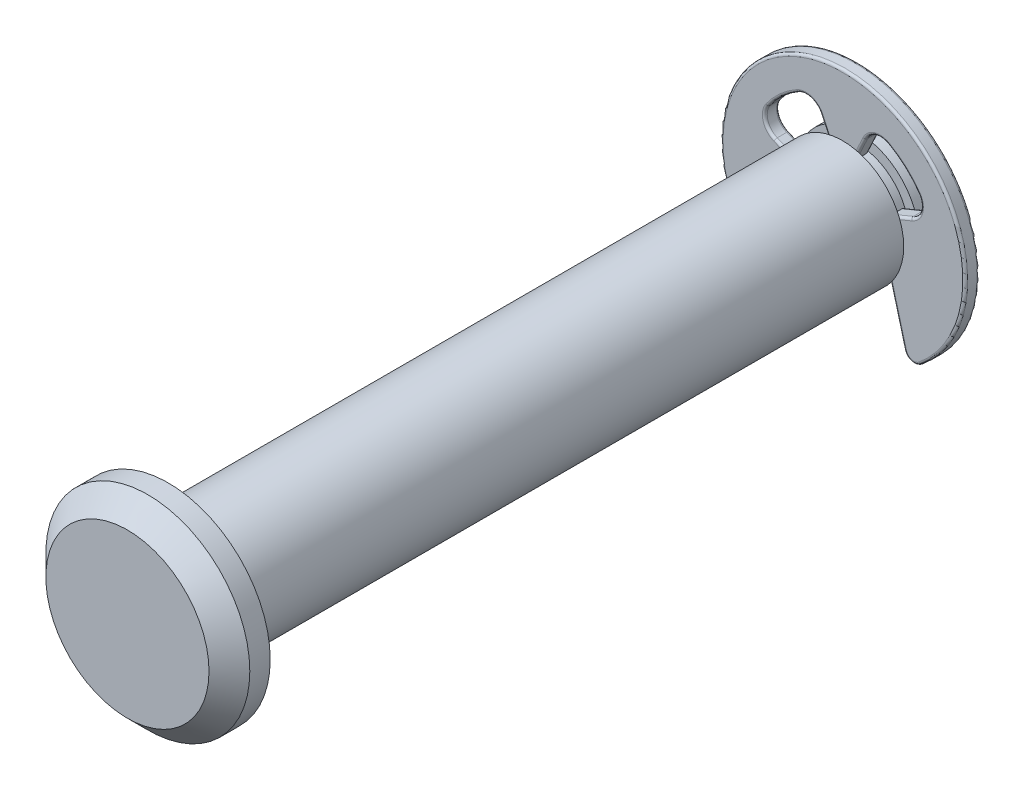
SolidWorks part; units mm, degrees
material "Plain Carbon Steel"
ref_plane "Front Plane" through (0, 0, 0) normal (0, 0, 1) x (1, 0, 0)
ref_plane "Top Plane" through (0, 0, 0) normal (0, 1, 0) x (1, 0, 0)
ref_plane "Right Plane" through (0, 0, 0) normal (1, 0, 0) x (0, 0, -1)
sketch "Sketch1" plane through (0, 0, 0) normal (1, 0, 0) x (0, 0, -1)
  line L0 (-17.5, 0) -> (17.5, 0) construction
  line L1 (-17.5, 0) -> (-19.5, 0) construction
  line L2 (-19.5, 0) -> (-19.5, 4)
  line L3 (-19.5, 4) -> (-18.5, 5)
  line L4 (-18.5, 5) -> (-17.5, 5)
  line L5 (-17.5, 5) -> (-17.5, 3)
  line L6 (-17.5, 3) -> (15.56, 3)
  line L7 (15.56, 3) -> (15.56, 2.5)
  line L8 (15.56, 2.5) -> (16.3, 2.5)
  line L9 (16.3, 2.5) -> (16.3, 3)
  line L10 (16.3, 3) -> (17.5, 3)
  line L11 (17.5, 3) -> (17.5, 0)
  line L12 (15.93, 2.5) -> (15.93, 3) construction
  line L13 (15.58, 0) -> (15.58, 6)
  line L14 (15.58, 6) -> (16.28, 6)
  line L15 (16.28, 6) -> (16.28, 0)
  dimension "Length" = 35
  dimension "Head Height" = 2
  dimension "D1" = 45
  dimension "Head Chamfer Length" = 1
  dimension "Groove Dia" = 5
  dimension "Dia" = 6
  dimension "Head Dia" = 10
  dimension "Ring Dia" = 12
  dimension "Ring Thickness" = 0.7
sketch "Sketch2" plane through (0, 0, 0) normal (1, 0, 0) x (0, 0, -1)
  line L0 (17.5, 3) -> (17.5, 0) construction
  line L1 (16.3, 3) -> (17.5, 3) construction
  line L2 (16.3, 2.5) -> (16.3, 3) construction
  line L3 (15.56, 2.5) -> (16.3, 2.5) construction
  line L4 (15.56, 3) -> (15.56, 2.5) construction
  line L5 (-17.5, 3) -> (15.56, 3) construction
  line L6 (-17.5, 5) -> (-17.5, 3) construction
  line L7 (-18.5, 5) -> (-17.5, 5) construction
  line L8 (-19.5, 4) -> (-18.5, 5) construction
  line L9 (-19.5, 0) -> (-19.5, 4) construction
  line L10 (17.5, 3) -> (17.5, 0)
  line L11 (16.3, 3) -> (17.5, 3)
  line L12 (16.3, 2.5) -> (16.3, 3)
  line L13 (15.56, 2.5) -> (16.3, 2.5)
  line L14 (15.56, 3) -> (15.56, 2.5)
  line L15 (-17.5, 3) -> (15.56, 3)
  line L16 (-17.5, 5) -> (-17.5, 3)
  line L17 (-18.5, 5) -> (-17.5, 5)
  line L18 (-19.5, 4) -> (-18.5, 5)
  line L19 (-19.5, 0) -> (-19.5, 4)
  line L20 (-19.5, 0) -> (17.5, 0)
revolve "Revolve1" add sketch "Sketch2" angle 360 about L0
ref_plane "Plane1" through (0, 0, -15.93) normal (0, 0, -1) x (-1, 0, 0)
sketch "Sketch3" plane through (0, 0, -15.93) normal (0, 0, -1) x (-1, 0, 0)
  line L6 (-1.0931, 3.5605) -> (-0.5681, 2.4346)
  line L7 (0.5681, 2.4346) -> (1.0931, 3.5605)
  line L8 (3.3375, 1.3824) -> (2.3097, 0.9567)
  line L9 (2.1614, -1.2563) -> (3, -4.386)
  line L10 (-3, -4.386) -> (-2.1614, -1.2563)
  line L11 (-2.3097, 0.9567) -> (-3.3375, 1.3824)
  line L12 (0, 0) -> (0, 4.5) construction
  line L13 (0, 0) -> (4.5, 0) construction
  arc A15 (-2.2113, 3.9192) -> (-3.6868, 2.5803) centre (0, 0) ccw
  arc A16 (-1.0931, 3.5605) -> (-2.2113, 3.9192) centre (-1.8182, 3.2225) ccw
  arc A19 (2.2113, 3.9192) -> (1.0931, 3.5605) centre (1.8182, 3.2225) ccw
  arc A20 (3.6868, 2.5803) -> (2.2113, 3.9192) centre (0, 0) ccw
  arc A21 (3.3375, 1.3824) -> (3.6868, 2.5803) centre (3.0313, 2.1215) ccw
  arc A22 (2.1614, -1.2563) -> (2.3097, 0.9567) centre (0, 0) ccw
  arc A23 (3, -4.386) -> (3.7996, -4.6436) centre (3.483, -4.2566) ccw
  arc A26 (-3.7996, -4.6436) -> (-3, -4.386) centre (-3.483, -4.2566) ccw
  arc A27 (-2.3097, 0.9567) -> (-2.1614, -1.2563) centre (0, 0) ccw
  arc A28 (-3.6868, 2.5803) -> (-3.3375, 1.3824) centre (-3.0313, 2.1215) ccw
  circle A30 centre (0, 0) radius 2.5
  circle A31 centre (0, 0) radius 6
  circle A32 centre (0, 0) radius 4.5 construction
  dimension "D1" = 9
  dimension "D6" = 0.5
  dimension "D7" = 0.8
  dimension "D2" = 30
  dimension "D3" = 50
  dimension "D4" = 97.5
  dimension "D8" = 97.5
  dimension "D5" = 6
  dimension "D9" = 3.6364
extrude "Boss-Extrude1" add sketch "Sketch3" along normal up to vertex (0.35 mm away) and the other way up to vertex (0.35 mm away) separate body contours A23 A31 A26 L10 A27 L11 A28 A15 A16 L6 A30 L7 A19 A20 A21 L8 A22 L9 up to point (0, 6, -16.28) other way up to point (0, 6, -15.58)
fillet "Fillet1" radius 0.12 36 edges at (0, 6, -15.58) (3.3297, -4.7326, -15.58) (2.5807, -2.8212, -15.58) (2.4944, -0.1672, -15.58) (2.8236, 1.1696, -15.58) (3.7994, 1.8976, -15.58) (3.0241, 3.3324, -15.58) (1.5738, 3.9842, -15.58) (0.8306, 2.9976, -15.58) (0, 2.5, -15.58) (-0.8306, 2.9976, -15.58) (-1.5738, 3.9842, -15.58) (-3.0241, 3.3324, -15.58) (-3.7994, 1.8976, -15.58) (-2.8236, 1.1696, -15.58) (-2.4944, -0.1672, -15.58) (-2.5807, -2.8212, -15.58) (-3.3297, -4.7326, -15.58) (-2.5807, -2.8212, -16.28) (-2.4944, -0.1672, -16.28) (-2.8236, 1.1696, -16.28) (-3.7994, 1.8976, -16.28) (-3.0241, 3.3324, -16.28) (-1.5738, 3.9842, -16.28) (-0.8306, 2.9976, -16.28) (0, 2.5, -16.28) (0.8306, 2.9976, -16.28) (1.5738, 3.9842, -16.28) (3.0241, 3.3324, -16.28) (3.7994, 1.8976, -16.28) (2.8236, 1.1696, -16.28) (2.4944, -0.1672, -16.28) (2.5807, -2.8212, -16.28) (3.3297, -4.7326, -16.28) (0, 6, -16.28) (-3.3297, -4.7326, -16.28)
chamfer "Chamfer1" distance 0.6 angle 45 1 edges at (3, 0, -17.5)
equation "\"D1@Sketch3\"=\"Ring Dia@Sketch1\"*.75"
equation "\"D6@Sketch3\" = \"Ring Dia@Sketch1\" / 24"
equation "\"D7@Sketch3\" = \"Ring Dia@Sketch1\" / 15"
equation "\"D5@Sketch3\" = \"Ring Dia@Sketch1\" / 2"
equation "\"D9@Sketch3\"= \"Ring Dia@Sketch1\" / 3.3"
equation "\"D1@Fillet1\"=\"Ring Dia@Sketch1\"*.01"
equation "\"D1@Chamfer1\"=\"Dia@Sketch1\"/10"
